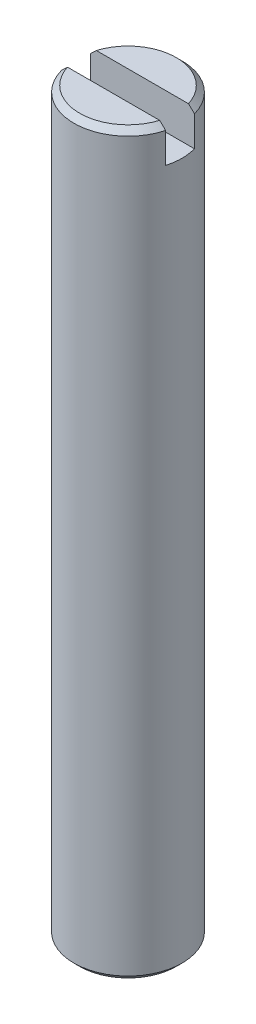
SolidWorks part; units mm, degrees
material "Plain Carbon Steel"
ref_plane "Front Plane" through (0, 0, 0) normal (0, 0, 1) x (1, 0, 0)
ref_plane "Top Plane" through (0, 0, 0) normal (0, 1, 0) x (1, 0, 0)
ref_plane "Right Plane" through (0, 0, 0) normal (1, 0, 0) x (0, 0, -1)
sketch "Sketch1" plane through (0, 0, 0) normal (0, 1, 0) x (1, 0, 0)
  circle A0 centre (0, 0) radius 4.7625
  dimension "D1" = 9.525
extrude "Boss-Extrude1" add sketch "Sketch1" along normal blind 65.1002
chamfer "Chamfer1" distance 0.508 angle 45 2 edges at (0, 0, 4.7625) (0, 65.1002, 4.7625)
sketch "Sketch2" plane through (0, 65.1002, 0) normal (0, 1, 0) x (1, 0, 0)
  line L1 (-4.5902, -1.27) -> (4.65, -1.27)
  line L3 (-4.6499, 1.27) -> (4.59, 1.27)
  line L5 (-4.5902, -1.27) -> (4.59, 1.27) construction
  line L6 (-4.6499, 1.27) -> (4.65, -1.27) construction
  circle A0 centre (0, 0) radius 4.7625 construction
  arc A1 (-4.6499, 1.27) -> (-4.5902, -1.27) centre (0.48, 0.1199) ccw
  circle A2 centre (0, 0) radius 4.7625
  circle A3 centre (0, 0) radius 4.7625
  arc A4 (4.59, 1.27) -> (4.65, -1.27) centre (-0.4312, -0.1193) cw
  point P0 (0, 0)
  circle M2 centre (0, 0) radius 4.2545
  dimension "D2" = 2.54
  dimension "D1" = 0
extrude "Cut-Extrude1" cut sketch "Sketch2" against normal blind 3.175 contours L3 L1 M2 | L3 A1 L1 M2 | L1 A3 L3 M2
